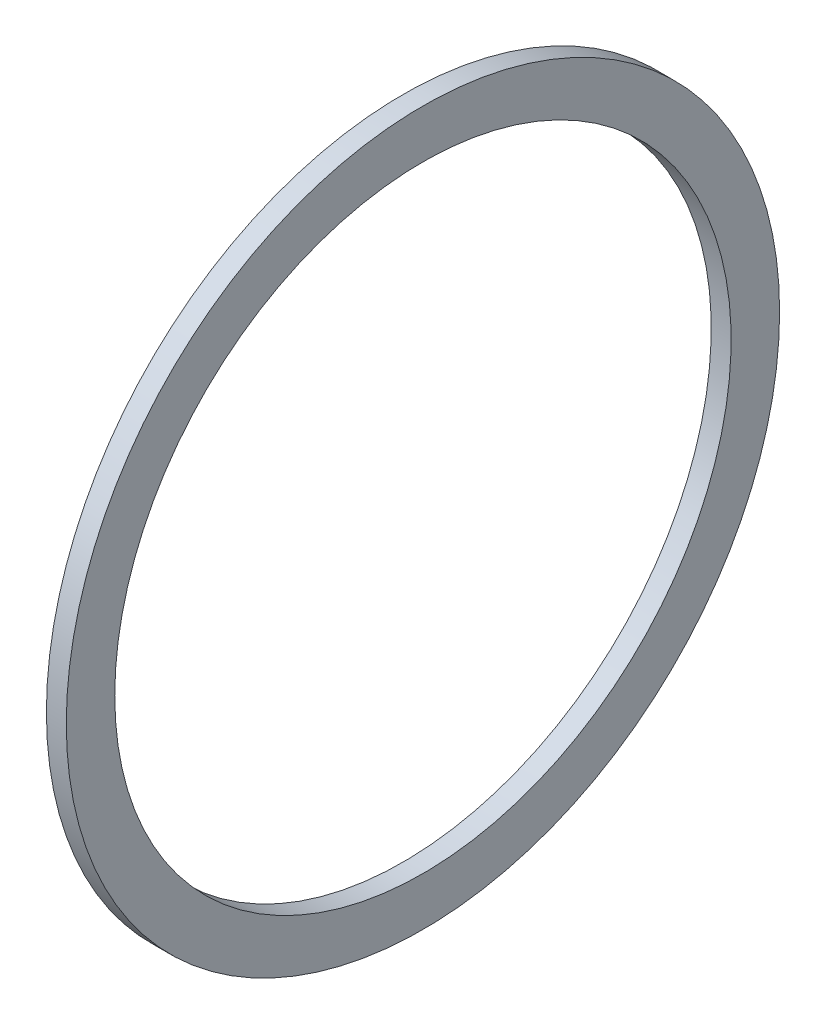
SolidWorks part; units mm, degrees
ref_plane "Front Plane" through (0, 0, 0) normal (0, 0, 1) x (1, 0, 0)
ref_plane "Top Plane" through (0, 0, 0) normal (0, 1, 0) x (1, 0, 0)
ref_plane "Right Plane" through (0, 0, 0) normal (1, 0, 0) x (0, 0, -1)
sketch "Sketch1" plane through (0, 0, 0) normal (0, 0, 1) x (1, 0, 0)
  line L0 (-43.7166, 0) -> (79.6876, 0) construction
  line L2 (0, -31.496) -> (2.032, -31.496)
  line L3 (0, -31.496) -> (0, -36.449)
  line L4 (0, -36.449) -> (2.032, -36.449)
  line L5 (2.032, -31.496) -> (2.032, -36.449)
  dimension "A" = 62.992
  dimension "B" = 72.898
  dimension "C" = 2.032
revolve "Revolve1" add sketch "Sketch1" angle 360 about L0
sketch "Sketch2" [suppressed] plane through (0, 0, 0) normal (0, 0, 1) x (1, 0, 0)
  line L0 (-34.685, 0) -> (47.6686, 0) construction
  circle A0 centre (2.54, -5.715) radius 0.762
  dimension "D1" = 2.54
  dimension "E" = 2.032
  dimension "D" = 54.864
revolve "Revolve3" [suppressed] add sketch "Sketch2" angle 360 about L0
